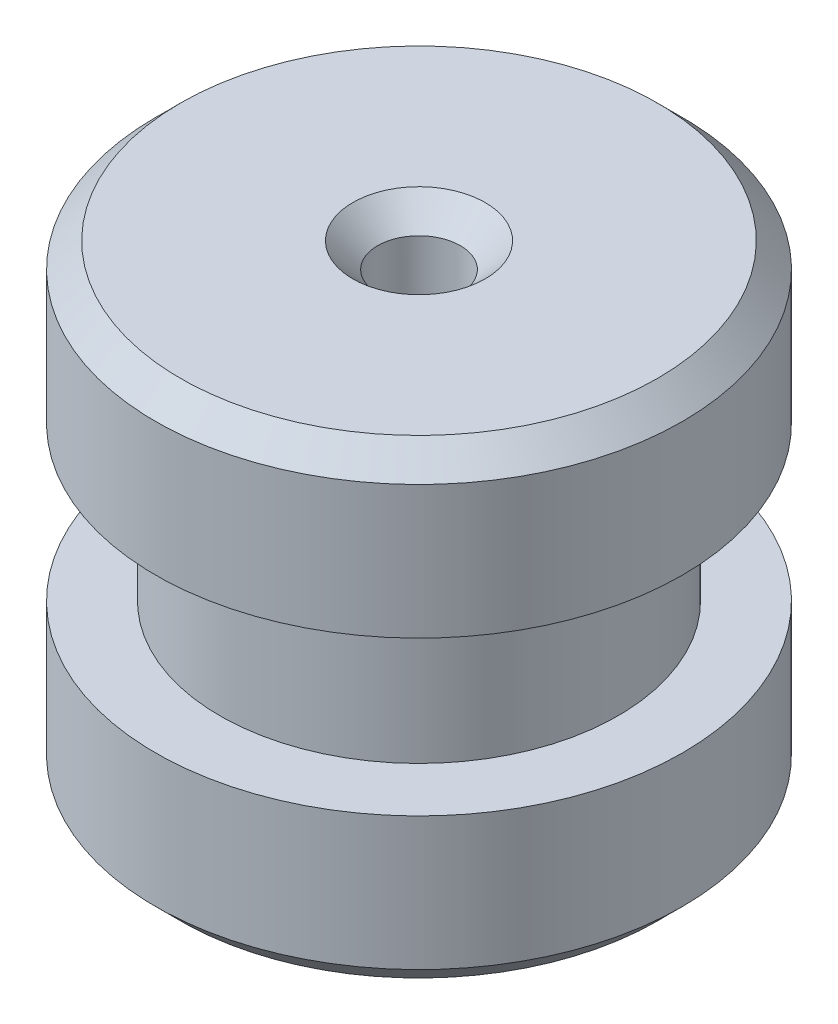
SolidWorks part; units mm, degrees
material "6061-T6 (SS)"
ref_plane "Front Plane" through (0, 0, 0) normal (0, 0, 1) x (1, 0, 0)
ref_plane "Top Plane" through (0, 0, 0) normal (0, 1, 0) x (1, 0, 0)
ref_plane "Right Plane" through (0, 0, 0) normal (1, 0, 0) x (0, 0, -1)
sketch "Sketch1" plane through (0, 0, 0) normal (0, 0, 1) x (1, 0, 0)
  line L0 (0, 14.16) -> (0, 0)
  line L5 (0, 0) -> (7.9375, 0)
  line L6 (7.9375, 0) -> (7.9375, 4.76)
  line L7 (7.9375, 4.76) -> (6, 4.76)
  line L8 (6, 4.76) -> (6, 9.4)
  line L9 (6, 9.4) -> (7.9375, 9.4)
  line L10 (7.9375, 9.4) -> (7.9375, 14.16)
  line L11 (7.9375, 14.16) -> (0, 14.16)
  line L12 (0, 14.16) -> (0, -19.2731) construction
  dimension "D1" = 12
  dimension "D3" = 15.875
  dimension "D4" = 4.76
  dimension "D5" = 4.64
  dimension "D6" = 4.76
revolve "Revolve1" add sketch "Sketch1" angle 360 about L12
sketch "Sketch2" plane through (0, 14.16, 0) normal (0, 1, 0) x (1, 0, 0)
  circle A0 centre (0, 0) radius 1.2446
  dimension "D1" = 2.4892
extrude "Cut-Extrude1" cut sketch "Sketch2" against normal through all
sketch "Sketch4" plane through (0, 0, 0) normal (0, -1, 0) x (1, 0, 0)
  circle A0 centre (0, 0) radius 2.5
  dimension "D1" = 5
extrude "Cut-Extrude3" cut sketch "Sketch4" against normal blind 6
chamfer "Chamfer1" distance 0.75 angle 45 3 edges at (-7.9375, 14.16, 0) (0, 14.16, 1.2446) (-7.9375, 0, 0)
